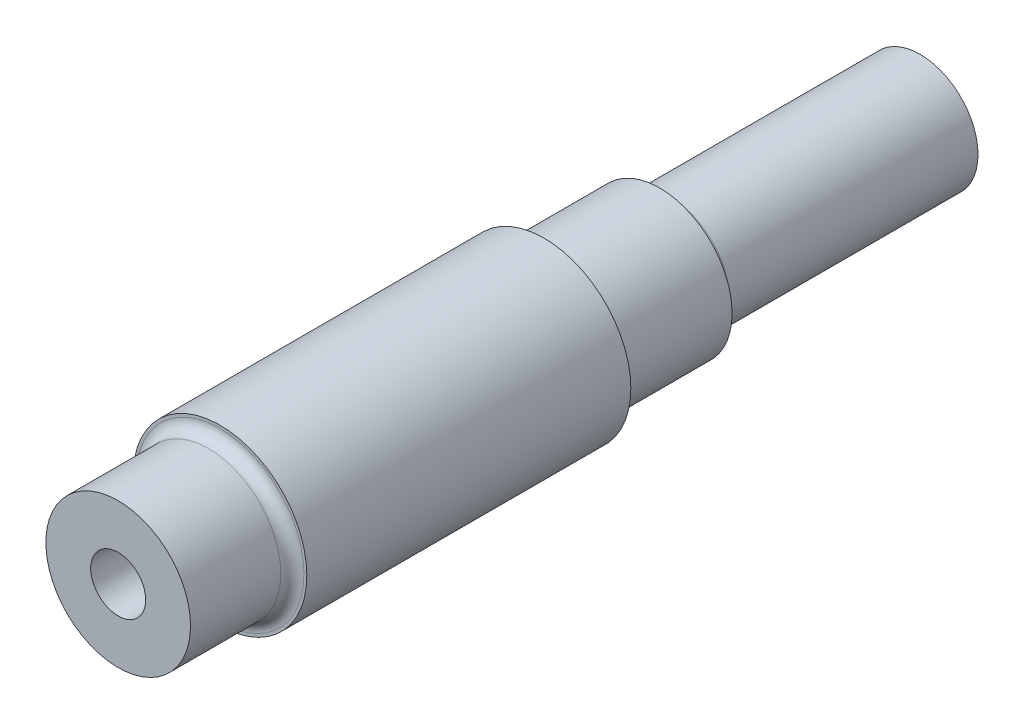
SolidWorks part; units mm, degrees
ref_plane "Front Plane" through (0, 0, 0) normal (0, 0, 1) x (1, 0, 0)
ref_plane "Top Plane" through (0, 0, 0) normal (0, 1, 0) x (1, 0, 0)
ref_plane "Right Plane" through (0, 0, 0) normal (1, 0, 0) x (0, 0, -1)
sketch "Sketch1" plane through (0, 0, 0) normal (0, 0, 1) x (1, 0, 0)
  circle A0 centre (0, 0) radius 12.5
  dimension "D1" = 25
extrude "Boss-Extrude1" add sketch "Sketch1" along normal blind 93.6
ref_plane "Plane1" through (0, 0, 76) normal (0, 0, 1) x (1, 0, 0)
sketch "Sketch2" plane through (0, 0, 76) normal (0, 0, 1) x (1, 0, 0)
  circle A0 centre (0, 0) radius 15
  dimension "D1" = 30
extrude "Boss-Extrude2" add sketch "Sketch2" against normal blind 56
sketch "Sketch3" plane through (0, 0, 0) normal (0, 0, -1) x (-1, 0, 0)
  circle A0 centre (0, 0) radius 10
extrude "Boss-Extrude3" add sketch "Sketch3" along normal blind 45
sketch "Sketch4" plane through (0, 0, 93.6) normal (0, 0, 1) x (1, 0, 0)
  circle A0 centre (0, 0) radius 4.755
  dimension "D1" = 9.51
extrude "Cut-Extrude1" cut sketch "Sketch4" against normal blind 60
fillet "Fillet2" radius 2 1 edges at (12.5, 0, 76)
fillet "Fillet3" radius 1.5 1 edges at (12.5, 0, 20)
fillet "Fillet4" radius 2 1 edges at (-10, 0, 0)
